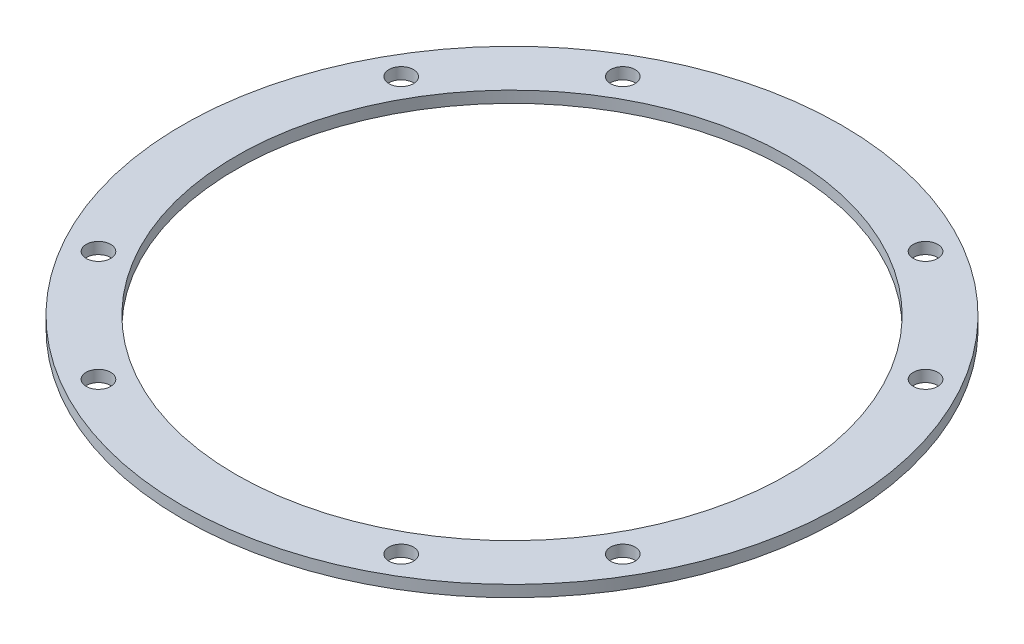
SolidWorks part; units mm, degrees
material "Thornel Mat VMA"
ref_plane "Front Plane" through (0, 0, 0) normal (0, 0, 1) x (1, 0, 0)
ref_plane "Top Plane" through (0, 0, 0) normal (0, 1, 0) x (1, 0, 0)
ref_plane "Right Plane" through (0, 0, 0) normal (1, 0, 0) x (0, 0, -1)
sketch "Sketch1" plane through (0, 0, 0) normal (0, 1, 0) x (1, 0, 0)
  circle A0 centre (0, 0) radius 43
  circle A1 centre (0, 0) radius 36
  dimension "D1" = 86
  dimension "D2" = 7
extrude "Boss-Extrude1" add sketch "Sketch1" along normal mid plane 1.5
hole_wizard "Ø3.2 (3.2) Diameter Hole1" positions "Sketch3" profile "Sketch2" hole size "Ø3.2" standard "ANSI Metric" end condition through all
sketch "Sketch3" plane through (0, 0.75, 0) normal (0, 1, 0) x (1, 0, 0)
  line L0 (0, 0) -> (-43, 0) construction
  line L3 (0, 0) -> (-37.2391, -21.5) construction
  line L6 (0, 0) -> (-37.2391, 21.5) construction
  circle A0 centre (0, 0) radius 43 construction
  point P22 (-34.208, -19.75)
  point P24 (-34.208, 19.75)
  point P31 (-19.75, 34.208)
  point P32 (19.75, 34.208)
  point P33 (34.208, 19.75)
  point P34 (34.208, -19.75)
  point P35 (19.75, -34.208)
  point P36 (-19.75, -34.208)
  point P37 (0, 0)
  dimension "D1" = 30
  dimension "D2" = 30
  dimension "D3" = 39.5
  dimension "D4" = 39.5
  dimension "D5" = 4
sketch "Sketch2" plane through (-34.208, 0.75, 19.75) normal (1, 0, 0) x (0, 0, 1)
  line L0 (0, 0) -> (0, 1.5)
  line L1 (0, 1.5) -> (1.6, 1.5)
  line L2 (1.6, 1.5) -> (1.6, 0)
  line L5 (1.6, 0) -> (0, 0)
  line L11 (0, -6.35) -> (0, 107.95) construction
  dimension "Thru Hole Dia." = 3.2
  dimension "Thru Hole Depth" = 1.5
